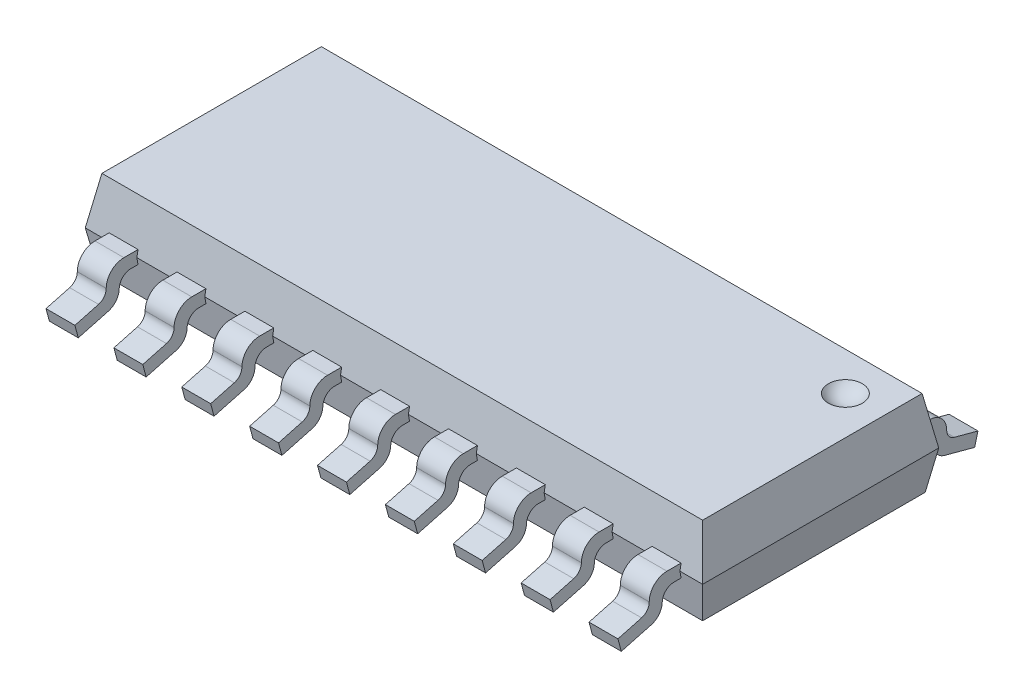
SolidWorks part; units mm, degrees
ref_plane "Front Plane" through (0, 0, 0) normal (0, 0, 1) x (1, 0, 0)
ref_plane "Top Plane" through (0, 0, 0) normal (0, 1, 0) x (1, 0, 0)
ref_plane "Right Plane" through (0, 0, 0) normal (1, 0, 0) x (0, 0, -1)
sketch "Sketch3" plane through (0, 0, 0) normal (1, 0, 0) x (0, 0, -1)
  line L0 (-2, 0) -> (2, 0) construction
  line L1 (-2, 0) -> (-1.8854, -0.65)
  line L2 (-1.8854, -0.65) -> (1.8854, -0.65)
  line L3 (1.8854, -0.65) -> (2, 0)
  line L4 (2, 0) -> (1.8589, 0.8)
  line L5 (1.8589, 0.8) -> (-1.8589, 0.8)
  line L6 (-1.8589, 0.8) -> (-2, 0)
  point P4 (0, 0)
  dimension "D1" = 4
  dimension "D2" = 1.45
  dimension "D3" = 0.65
  dimension "D4" = 100
  dimension "D5" = 100
  dimension "D6" = 100
  dimension "D7" = 100
extrude "Boss-Extrude1" add sketch "Sketch3" along normal mid plane 10.46
sketch "Sketch4" plane through (0, 0, 0) normal (0, 0, 1) x (1, 0, 0)
  line L0 (-5.23, 0) -> (-5.0889, 0.8)
  line L1 (5.23, 0.8) -> (-5.23, 0.8) construction
  line L2 (-5.0889, 0.8) -> (-6, 0.8)
  line L3 (-5.23, 0) -> (-5.1154, -0.65)
  line L4 (5.23, -0.65) -> (-5.23, -0.65) construction
  line L5 (-5.1154, -0.65) -> (-6, -0.65)
  line L6 (-6, -0.65) -> (-6, 0.8)
  line L7 (0, 0) -> (0, 1.6058) construction
  line L8 (6, -0.65) -> (6, 0.8)
  line L9 (5.1154, -0.65) -> (6, -0.65)
  line L10 (5.23, 0) -> (5.1154, -0.65)
  line L11 (5.0889, 0.8) -> (6, 0.8)
  line L12 (5.23, 0) -> (5.0889, 0.8)
  dimension "D1" = 80
  dimension "D2" = 80
  dimension "D3" = 6
extrude "Cut-Extrude1" cut sketch "Sketch4" against normal mid plane 8.75
ref_plane "Plane1" through (0, 1, 0) normal (0, 1, 0) x (1, 0, 0)
sketch "Sketch8" plane through (0, 0, 0) normal (1, 0, 0) x (0, 0, -1)
  line L0 (-2, 0) -> (-2.3016, 0) construction
  line L1 (-2, 0) -> (-1.9806, 0.11)
  line L2 (-2, 0) -> (-1.8589, 0.8) construction
  line L3 (-1.9806, 0.11) -> (-2.22, 0.11)
  line L4 (-2.6496, -0.3602) -> (-3.05, -0.4675)
  line L5 (-3.05, -0.4675) -> (-2.9931, -0.68)
  line L6 (-2.9931, -0.68) -> (-2.4853, -0.5439)
  line L7 (-2.3, -0.3025) -> (-2.3, -0.31)
  line L8 (-2.1, -0.11) -> (-1.9806, -0.11)
  line L9 (-1.8854, -0.65) -> (-2, 0) construction
  line L10 (-1.9806, -0.11) -> (-2, 0)
  line L11 (-2.52, -0.19) -> (-2.52, -0.1913)
  arc A0 (-2.22, 0.11) -> (-2.52, -0.19) centre (-2.22, -0.19) ccw
  arc A2 (-2.52, -0.1913) -> (-2.6496, -0.3602) centre (-2.6949, -0.1913) cw
  arc A3 (-2.4853, -0.5439) -> (-2.3, -0.3025) centre (-2.55, -0.3025) ccw
  arc A5 (-2.3, -0.31) -> (-2.1, -0.11) centre (-2.1, -0.31) cw
  dimension "D4" = 0.25
  dimension "D6" = 0.2
  dimension "D8" = 0.3
  dimension "D1" = 1.05
  dimension "D2" = 0.22
  dimension "D3" = 0.75
  dimension "D5" = 0.22
  dimension "D7" = 0.22
  dimension "D9" = 105
  dimension "D10" = 0.68
extrude "Boss-Extrude3" add sketch "Sketch8" along normal mid plane 0.49
sketch "Sketch9" plane through (0, 1, 0) normal (0, 1, 0) x (1, 0, 0)
  line L0 (5.0889, 1.8589) -> (-5.0889, 1.8589) construction
  line L1 (5.0889, 1.8589) -> (5.0889, -1.8589) construction
  line L2 (4.7889, 1.2089) -> (4.0889, 1.2089)
  arc A0 (4.7889, 1.2089) -> (4.0889, 1.2089) centre (4.4389, 1.2089) ccw
  dimension "D3" = 0.7
  dimension "D1" = 0.65
  dimension "D2" = 0.65
revolve "Cut-Revolve1" cut sketch "Sketch9" angle 360 about L2
pattern_linear "LPattern1" count 5 spacing 1.15 along (1, 0, 0) count 5 spacing 1.15 along (-1, 0, 0) of "Boss-Extrude3"
mirror "Mirror1" about plane through (0, 0, 0) normal (0, 0, 1) of "Boss-Extrude3", "LPattern1"
